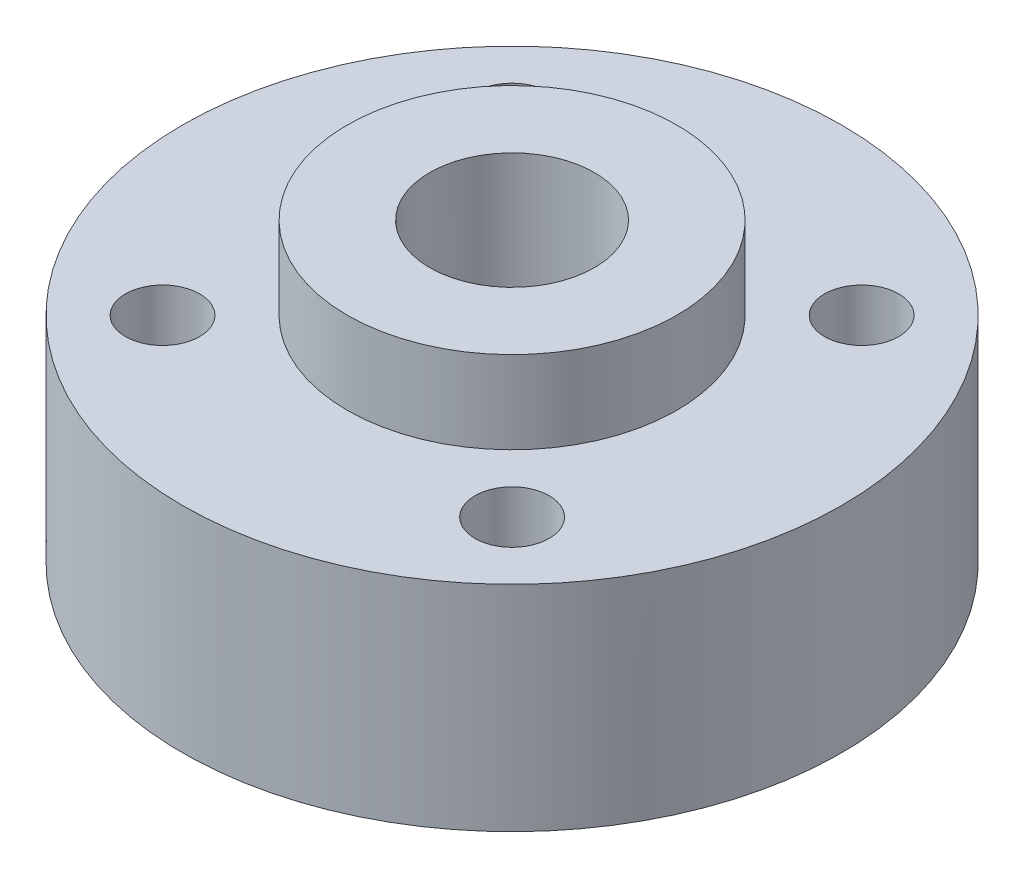
SolidWorks part; units mm, degrees
ref_plane "Front Plane" through (0, 0, 0) normal (0, 0, 1) x (1, 0, 0)
ref_plane "Top Plane" through (0, 0, 0) normal (0, 1, 0) x (1, 0, 0)
ref_plane "Right Plane" through (0, 0, 0) normal (1, 0, 0) x (0, 0, -1)
sketch "Sketch1" plane through (0, 0, 0) normal (0, 1, 0) x (1, 0, 0)
  circle A0 centre (0, 0) radius 20
  circle A1 centre (0, 0) radius 5
  dimension "D1" = 40
  dimension "D2" = 10
extrude "Boss-Extrude1" add sketch "Sketch1" along normal mid plane 15
sketch "Sketch2" plane through (0, 7.5, 0) normal (0, 1, 0) x (1, 0, 0)
  line L0 (0, 0) -> (0, 20) construction
  line L1 (0, 0) -> (-10.6066, 10.6066) construction
  circle A0 centre (0, 0) radius 20 construction
  circle A1 centre (-10.6066, 10.6066) radius 2.25
  dimension "D1" = 4.5
  dimension "D2" = 15
  dimension "D3" = 45
extrude "Cut-Extrude1" cut sketch "Sketch2" against normal blind 12
pattern_circular "CirPattern1" count 4 over 360 about axis through (0, 0, 0) along (0, 1, 0) of "Cut-Extrude1"
sketch "Sketch3" plane through (0, 0, 0) normal (0, 0, 1) x (1, 0, 0)
  line L0 (0, 7.5) -> (0, -7.5) construction
  line L1 (5, 7.5) -> (-5, 7.5) construction
  line L2 (-20, -7.5) -> (20, -7.5) construction
  circle A0 centre (0, 0) radius 2.25
  dimension "D1" = 4.5
extrude "Cut-Extrude2" cut sketch "Sketch3" against normal through all
pattern_circular "CirPattern2" count 2 every 90 about axis through (0, 7.5, 0) along (0, 1, 0) of "Cut-Extrude2"
sketch "Sketch4" plane through (0, -7.5, 0) normal (0, -1, 0) x (1, 0, 0)
  circle A0 centre (0, 0) radius 23.7085
  circle A1 centre (0, 0) radius 10
  dimension "D1" = 20
extrude "Cut-Extrude3" cut sketch "Sketch4" against normal blind 2
sketch "Sketch5" plane through (0, 7.5, 0) normal (0, 1, 0) x (1, 0, 0)
  circle A0 centre (0, 0) radius 5
  circle A1 centre (0, 0) radius 10
  dimension "D1" = 20
extrude "Boss-Extrude2" add sketch "Sketch5" along normal blind 5
